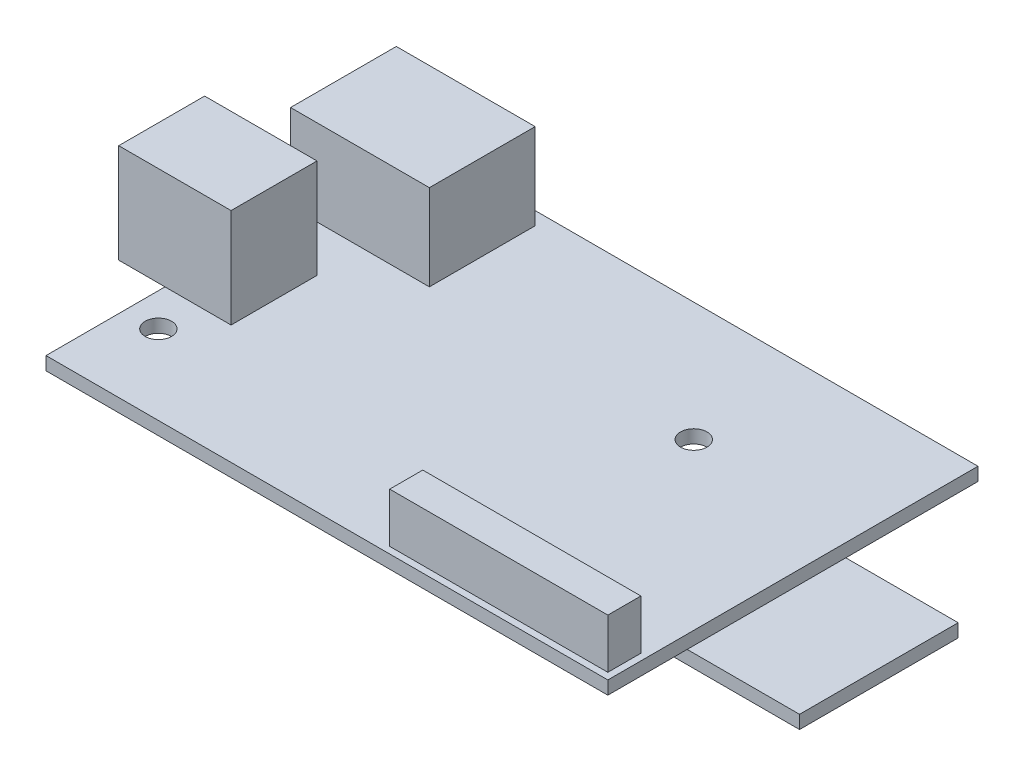
SolidWorks part; units mm, degrees
ref_plane "Front" through (0, 0, 0) normal (0, 0, 1) x (1, 0, 0)
ref_plane "Top" through (0, 0, 0) normal (0, 1, 0) x (1, 0, 0)
ref_plane "Right" through (0, 0, 0) normal (1, 0, 0) x (0, 0, -1)
sketch "Sketch1" plane through (0, 0, 0) normal (0, 1, 0) x (1, 0, 0)
  line L1 (0, 0) -> (85, 0)
  line L2 (0, 0) -> (0, 56)
  line L3 (0, 56) -> (85, 56)
  line L4 (85, 0) -> (85, 56)
  dimension "D1" = 85
  dimension "D2" = 56
extrude "Boss-Extrude1" add sketch "Sketch1" along normal blind 2
sketch "Sketch2" plane through (0, 2, 0) normal (0, 1, 0) x (1, 0, 0)
  line L0 (0, 56) -> (0, 0) construction
  line L1 (-1, 54) -> (20, 54)
  line L2 (-1, 54) -> (-1, 38)
  line L3 (-1, 38) -> (20, 38)
  line L4 (20, 54) -> (20, 38)
  line L5 (85, 56) -> (0, 56) construction
  dimension "D1" = 16
  dimension "D2" = 21
  dimension "D3" = 1
  dimension "D4" = 2
extrude "Boss-Extrude2" add sketch "Sketch2" along normal blind 13
sketch "Sketch3" plane through (0, 2, 0) normal (0, 1, 0) x (1, 0, 0)
  line L0 (0, 38) -> (0, 0) construction
  line L1 (-7, 31) -> (10, 31)
  line L2 (-7, 31) -> (-7, 18)
  line L3 (-7, 18) -> (10, 18)
  line L4 (10, 31) -> (10, 18)
  line L5 (0, 38) -> (20, 38) construction
  dimension "D1" = 13
  dimension "D2" = 17
  dimension "D3" = 7
  dimension "D4" = 7
extrude "Boss-Extrude3" add sketch "Sketch3" along normal blind 15
sketch "Sketch4" plane through (0, 0, 0) normal (0, -1, 0) x (1, 0, 0)
  line L0 (85, -56) -> (0, -56) construction
  line L1 (69, -12) -> (102, -12)
  line L2 (69, -12) -> (69, -36)
  line L3 (69, -36) -> (102, -36)
  line L4 (102, -12) -> (102, -36)
  line L5 (85, 0) -> (85, -56) construction
  dimension "D1" = 33
  dimension "D2" = 24
  dimension "D3" = 20
  dimension "D4" = 17
extrude "Boss-Extrude4" add sketch "Sketch4" along normal blind 2
sketch "Sketch5" plane through (0, 2, 0) normal (0, 1, 0) x (1, 0, 0)
  line L0 (0, 18) -> (0, 0) construction
  line L1 (0, 0) -> (85, 0) construction
  line L2 (85, 56) -> (0, 56) construction
  line L3 (85, 0) -> (85, 56) construction
  circle A0 centre (5, 12) radius 2
  circle A1 centre (60, 38) radius 2
  dimension "D1" = 4
  dimension "D2" = 4
  dimension "D3" = 5
  dimension "D4" = 12
  dimension "D5" = 18
  dimension "D6" = 25
extrude "Cut-Extrude1" cut sketch "Sketch5" against normal up to next
sketch "Sketch6" plane through (0, 2, 0) normal (0, 1, 0) x (1, 0, 0)
  line L0 (85, 0) -> (85, 56) construction
  line L1 (51, 6) -> (84, 6)
  line L2 (51, 6) -> (51, 1)
  line L3 (51, 1) -> (84, 1)
  line L4 (84, 6) -> (84, 1)
  line L5 (0, 0) -> (85, 0) construction
  dimension "D1" = 33
  dimension "D2" = 5
  dimension "D3" = 1
  dimension "D4" = 1
extrude "Boss-Extrude5" add sketch "Sketch6" along normal blind 7.5
